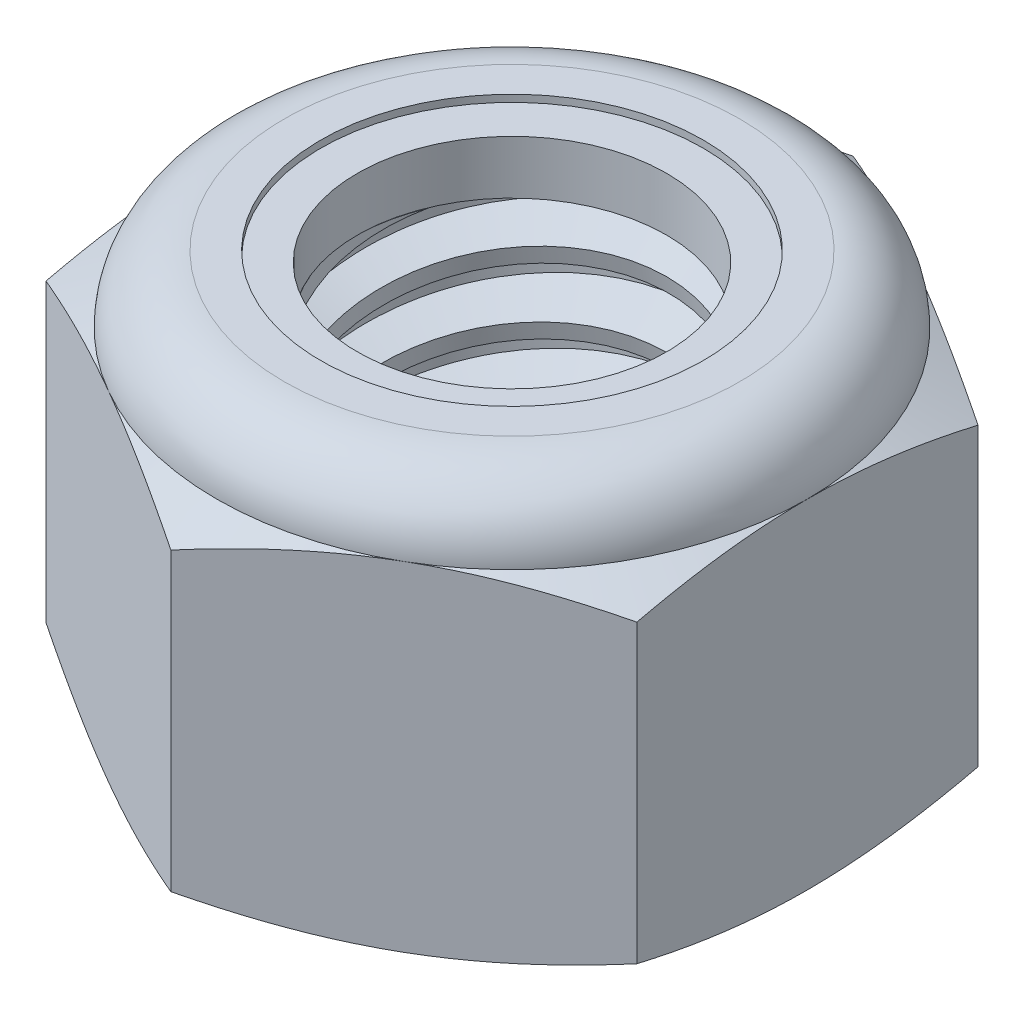
SolidWorks part; units mm, degrees
material "Plain Carbon Steel"
ref_plane "Front" through (0, 0, 0) normal (0, 0, 1) x (1, 0, 0)
ref_plane "Top" through (0, 0, 0) normal (0, 1, 0) x (1, 0, 0)
ref_plane "Right" through (0, 0, 0) normal (1, 0, 0) x (0, 0, -1)
sketch "Sketch1" plane through (0, 0, 0) normal (0, 1, 0) x (1, 0, 0)
  line L1 (0, 7.3323) -> (-6.35, 3.6662)
  line L2 (-6.35, 3.6662) -> (-6.35, -3.6662)
  line L3 (-6.35, -3.6662) -> (0, -7.3323)
  line L4 (0, -7.3323) -> (6.35, -3.6662)
  line L5 (6.35, -3.6662) -> (6.35, 3.6662)
  line L6 (6.35, 3.6662) -> (0, 7.3323)
  circle A0 centre (0, 0) radius 6.35 construction
  dimension "Hex Flats" = 12.7
extrude "Extrude1" add sketch "Sketch1" along normal blind 8.7312
sketch "Sketch2" plane through (0, 0, 0) normal (1, 0, 0) x (0, 0, -1)
  line L0 (-3.9688, 0) -> (-3.9688, 8.7312) construction
  line L1 (0, 0) -> (3.9688, 0)
  line L2 (0, 0) -> (0, 8.7312)
  line L3 (0, 8.7312) -> (3.9688, 8.7312)
  line L4 (3.9688, 0) -> (3.9688, 8.7312)
  line L5 (-3.6662, 8.7312) -> (3.6662, 8.7312) construction
  line L7 (0, -3.9688) -> (0, 0) construction
  dimension "Thread Dia" = 7.9375
revolve "Revolve1" add sketch "Sketch2" angle 360 about L7
sketch "Sketch3" plane through (0, 0, 0) normal (1, 0, 0) x (0, 0, -1)
  line L0 (3.9688, 8.7312) -> (-3.9687, 8.7312) construction
  line L1 (-3.9687, 8.7312) -> (-3.9688, 7.3201) construction
  line L2 (-3.9688, 7.3201) -> (3.9688, 8.7312) construction
  line L3 (3.9688, 8.7312) -> (3.9996, 8.5576) construction
  line L4 (3.9996, 8.5576) -> (4.2157, 7.3419)
  line L5 (4.2157, 7.3419) -> (3.3866, 7.6424)
  line L6 (3.3866, 7.6424) -> (3.3248, 7.9897)
  line L7 (3.3248, 7.9897) -> (3.9996, 8.5576)
  line L8 (3.3557, 7.8161) -> (4.1077, 7.9498) construction
  line L9 (3.9688, 8.7312) -> (3.9688, 7.9251) construction
  line L10 (3.9688, 7.9251) -> (-3.9688, 6.5139) construction
  line L11 (-3.9688, 6.5139) -> (-3.9688, 7.3201) construction
  line L12 (-0.2688, 8.7312) -> (0.2688, 5.7077) construction
  line L13 (-3.9688, 0) -> (-3.9688, 8.7312) construction
  line L14 (0, 8.7312) -> (3.9688, 8.7312) construction
  line L15 (3.9688, 0) -> (3.9688, 8.7312) construction
  point P13 (0, 7.2195)
  dimension "D1" = 0.1764
  dimension "D2" = 0.3528
  dimension "Thread Pitch" = 1.4111
  dimension "D4" = 60
  dimension "D5" = 1.4111
revolve "Cut-Revolve1" cut sketch "Sketch3" angle 360 about L12
pattern_linear "LPattern1" count 6 spacing 1.4111 along (0, 1, 0) count 2 spacing 1.4111 along (0, 1, 0) of "Cut-Revolve1"
sketch "Sketch4" plane through (0, 0, 0) normal (1, 0, 0) x (0, 0, -1)
  line L0 (0, 8.7312) -> (3.9688, 8.7312)
  line L1 (3.9688, 8.7312) -> (3.3248, 8.431)
  line L2 (3.3248, 8.431) -> (3.3248, 0.3003)
  line L3 (3.3248, 0.3003) -> (3.9688, 0)
  line L4 (3.9688, 0) -> (0, 0)
  line L5 (0, 0) -> (0, 8.7312)
  line L6 (3.9688, 0) -> (3.9688, 8.7312) construction
  line L7 (0, 8.7312) -> (3.9688, 8.7312) construction
  line L8 (0, 0) -> (3.9688, 0) construction
  line L9 (0, 0) -> (0, 8.7312) construction
  line L10 (0, 8.7312) -> (0, 9.4418) construction
  dimension "D1" = 25
revolve "Cut-Revolve2" cut sketch "Sketch4" angle 360 about L10
combine bodies "Combine1" operation type subtract main body 112 bodies to subtract 111
sketch "Sketch5" plane through (0, 0, 0) normal (1, 0, 0) x (0, 0, -1)
  line L0 (0, 0) -> (6.35, 0)
  line L1 (6.35, 0) -> (7.3323, 0.4581)
  line L2 (7.3323, 0.4581) -> (7.3323, 6.818)
  line L3 (7.3323, 6.818) -> (6.35, 7.276)
  line L4 (4.8948, 8.7312) -> (4.8948, 10.0012)
  line L5 (4.8948, 10.0012) -> (8.6023, 10.0012)
  line L6 (8.6023, 10.0012) -> (8.6023, -1.27)
  line L7 (8.6023, -1.27) -> (0, -1.27)
  line L8 (0, -1.27) -> (0, 0)
  line L9 (6.35, 7.276) -> (6.35, 0) construction
  line L10 (0, 0) -> (3.9688, 0) construction
  line L13 (7.3323, 3.638) -> (8.6023, 3.638) construction
  line L14 (7.3323, 8.7312) -> (7.3323, 0) construction
  line L15 (0, 0) -> (0, 10.0012) construction
  line L20 (0, 10.0012) -> (4.8948, 10.0012) construction
  line L22 (0, 8.7312) -> (3.9688, 8.7312) construction
  arc A0 (6.35, 7.276) -> (4.8948, 8.7312) centre (4.8948, 7.276) ccw
  dimension "D1" = 25
  dimension "D2" = 1.27
  dimension "D3" = 8.7312
  dimension "D4" = 1.4552
revolve "Cut-Revolve3" cut sketch "Sketch5" angle 360 about L15
sketch "Sketch6" plane through (0, 0, 0) normal (1, 0, 0) x (0, 0, -1)
  line L0 (0, 7.276) -> (6.1976, 7.276)
  line L1 (4.8948, 8.5788) -> (4.1098, 8.5788)
  line L2 (0, 10.0012) -> (0, 7.276)
  line L3 (4.1098, 10.0012) -> (0, 10.0012)
  line L4 (0, 10.0012) -> (4.8948, 10.0012) construction
  line L5 (0, 0) -> (0, 10.0012) construction
  line L6 (0, 10.0012) -> (0, 44.323) construction
  line L7 (4.1098, 8.5788) -> (4.1098, 10.0012)
  line L8 (4.8948, 8.7312) -> (4.8948, 8.5788) construction
  line L9 (4.1098, 8.5788) -> (3.3248, 8.5788) construction
  line L10 (3.3248, 8.5788) -> (3.3248, 8.431) construction
  arc A0 (6.1976, 7.276) -> (4.8948, 8.5788) centre (4.8948, 7.276) ccw
  arc A1 (6.35, 7.276) -> (4.8948, 8.7312) centre (4.8948, 7.276) ccw construction
  dimension "D1" = 0.1524
revolve "Cut-Revolve4" cut sketch "Sketch6" angle 360 about L6
sketch "Sketch7" plane through (0, 0, 0) normal (1, 0, 0) x (0, 0, -1)
  line L0 (3.3248, 7.3522) -> (6.119, 7.3522)
  line L1 (4.8948, 8.5027) -> (3.3248, 8.5027)
  line L2 (3.3248, 8.5027) -> (3.3248, 7.3522)
  line L3 (3.3248, 7.3522) -> (0, 7.3522) construction
  line L4 (0, 7.3522) -> (0, 8.5027) construction
  line L5 (0, 8.5027) -> (3.3248, 8.5027) construction
  line L6 (3.3248, 7.3522) -> (3.3248, 7.276) construction
  line L7 (0, 7.276) -> (6.1976, 7.276) construction
  line L8 (4.8948, 8.5027) -> (4.8948, 8.5788) construction
  arc A0 (6.119, 7.3522) -> (4.8948, 8.5027) centre (4.8948, 7.276) ccw
  arc A2 (6.1976, 7.276) -> (4.8948, 8.5788) centre (4.8948, 7.276) ccw construction
  dimension "D1" = 0.0762
revolve "Revolve2" add sketch "Sketch7" angle 360 about L4
equation "\"D1@Sketch3\"=\"Thread Pitch@Sketch3\"/8"
equation "\"D2@Sketch3\"=\"Thread Pitch@Sketch3\"/4"
equation "\"D5@Sketch3\"=\"Thread Pitch@Sketch3\""
equation "\"D4@LPattern1\"=\"Thread Pitch@Sketch3\""
equation "\"D3@LPattern1\"=\"Thread Pitch@Sketch3\""
equation "\"D1@LPattern1\"=\"Height@Extrude1\"/\"Thread Pitch@Sketch3\""
equation "\"D4@Sketch5\"=\"Height@Extrude1\"/6"
